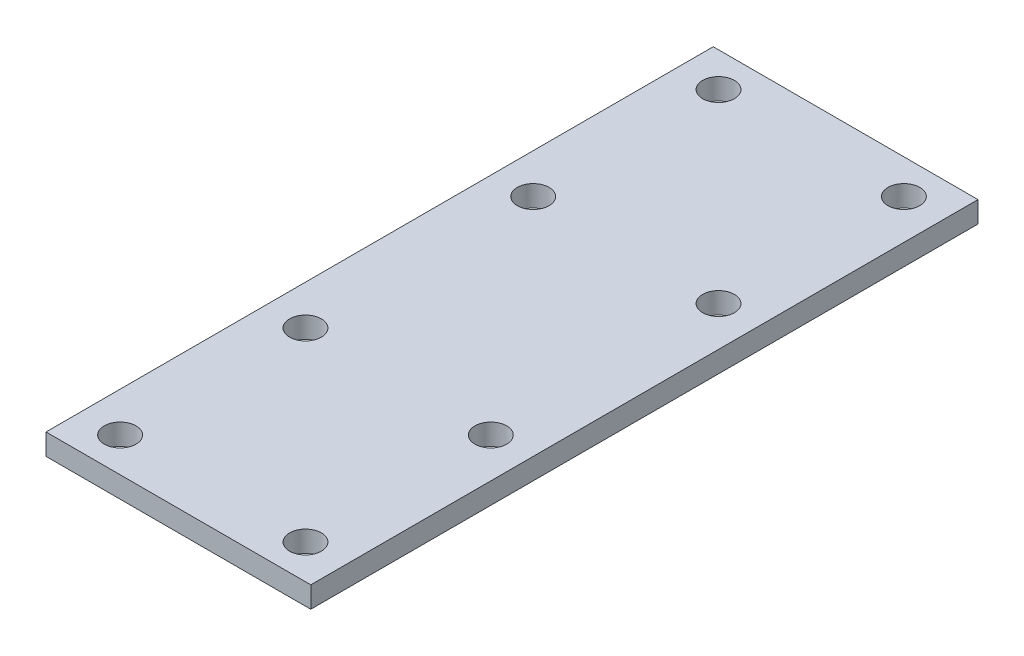
SolidWorks part; units mm, degrees
ref_plane "Front Plane" through (0, 0, 0) normal (0, 0, 1) x (1, 0, 0)
ref_plane "Top Plane" through (0, 0, 0) normal (0, 1, 0) x (1, 0, 0)
ref_plane "Right Plane" through (0, 0, 0) normal (1, 0, 0) x (0, 0, -1)
sketch "Sketch1" plane through (0, 0, 0) normal (0, 1, 0) x (1, 0, 0)
  line L0 (0, 37.8806) -> (0, -40.4305) construction
  line L1 (-72.1679, 0) -> (75.3748, 0) construction
  line L2 (0, 63) -> (50, 63) construction
  line L3 (0, 0) -> (50, 0)
  line L4 (0, 0) -> (0, 126)
  line L5 (0, 126) -> (50, 126)
  line L6 (50, 0) -> (50, 126)
  line L7 (25, 126) -> (25, 0) construction
  circle A0 centre (7.5, 119.5) radius 3
  circle A1 centre (7.5, 84.5) radius 3
  circle A2 centre (42.5, 84.5) radius 3
  circle A3 centre (42.5, 119.5) radius 3
  circle A4 centre (7.5, 41.5) radius 3
  circle A5 centre (7.5, 6.5) radius 3
  circle A6 centre (42.5, 6.5) radius 3
  circle A7 centre (42.5, 41.5) radius 3
  dimension "D2" = 126
  dimension "D4" = 6
  dimension "D1" = 50
  dimension "D3" = 35
  dimension "D5" = 6.5
  dimension "D6" = 7.5
  dimension "D7" = 7.5
extrude "Boss-Extrude1" add sketch "Sketch1" along normal blind 4
sketch "Sketch2" plane through (0, 4, 0) normal (0, 1, 0) x (1, 0, 0)
  line L0 (25, 126) -> (25, 0) construction
  line L1 (50, 126) -> (0, 126) construction
  line L2 (0, 0) -> (50, 0) construction
  line L3 (0, 63) -> (50, 63) construction
  line L4 (0, 126) -> (0, 0) construction
  line L5 (50, 0) -> (50, 126) construction
  circle A0 centre (6.5, 63) radius 2.5
  circle A1 centre (43.5, 63) radius 2.5
  circle A2 centre (25, 63) radius 6
  dimension "D1" = 5
  dimension "D3" = 12
  dimension "D2" = 37
